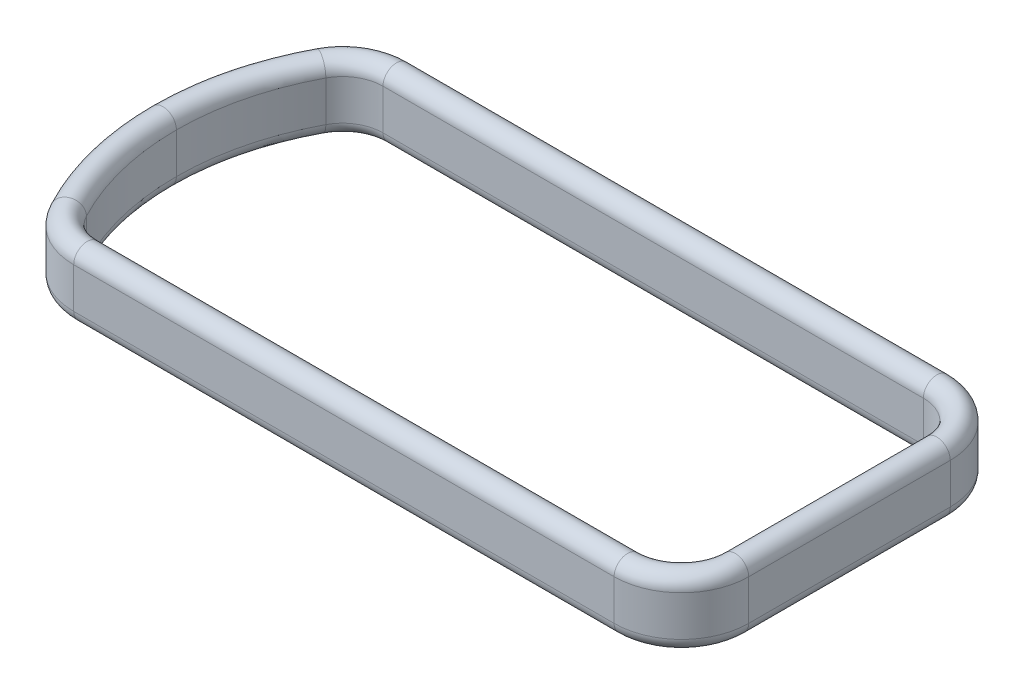
SolidWorks part; units mm, degrees
ref_plane "Vorne" through (0, 0, 0) normal (0, 0, 1) x (1, 0, 0)
ref_plane "Oben" through (0, 0, 0) normal (0, 1, 0) x (1, 0, 0)
ref_plane "Rechts" through (0, 0, 0) normal (1, 0, 0) x (0, 0, -1)
sketch "Skizze1" plane through (0, 0, 0) normal (0, 1, 0) x (1, 0, 0)
  line L1 (-100.351, -57.4328) -> (100.351, -57.4328)
  line L3 (-100.351, 57.4328) -> (100.351, 57.4328)
  line L4 (120.351, -37.4328) -> (120.351, 37.4328)
  line L5 (0, 57.4328) -> (0, -57.4328) construction
  line L6 (-107.3009, 0) -> (120.351, 0) construction
  arc A0 (-100.351, -57.4328) -> (-118.0266, -46.791) centre (-100.351, -37.4328) cw
  arc A1 (100.351, 57.4328) -> (120.351, 37.4328) centre (100.351, 37.4328) cw
  arc A2 (100.351, -57.4328) -> (120.351, -37.4328) centre (100.351, -37.4328) ccw
  arc A3 (-118.0266, 46.791) -> (-100.351, 57.4328) centre (-100.351, 37.4328) cw
  arc A4 (-118.0266, -46.791) -> (-118.0266, 46.791) centre (-29.649, 0) cw
  point P0 (0, 0)
  dimension "D1" = 20
  dimension "D2" = 100
  dimension "D3" = 114.8656
  dimension "D4" = 150
sketch "Skizze2" plane through (0, 0, 0) normal (0, 0, 1) x (1, 0, 0)
  line L2 (-129.649, 0) -> (-129.649, -15) construction
  line L6 (-124.649, 0) -> (-124.649, -15)
  line L7 (-134.649, 0) -> (-134.649, -15)
  line L10 (-107.3009, 0) -> (120.351, 0) construction
  arc A0 (-124.649, 0) -> (-134.649, 0) centre (-129.649, 0) ccw
  arc A1 (-134.649, -15) -> (-124.649, -15) centre (-129.649, -15) ccw
  point P2 (-129.649, -7.5)
  dimension "D2" = 5
  dimension "D1" = 90
  dimension "D3" = 15
sweep "Austragung1" add profiles "Skizze2" path "Skizze1"
